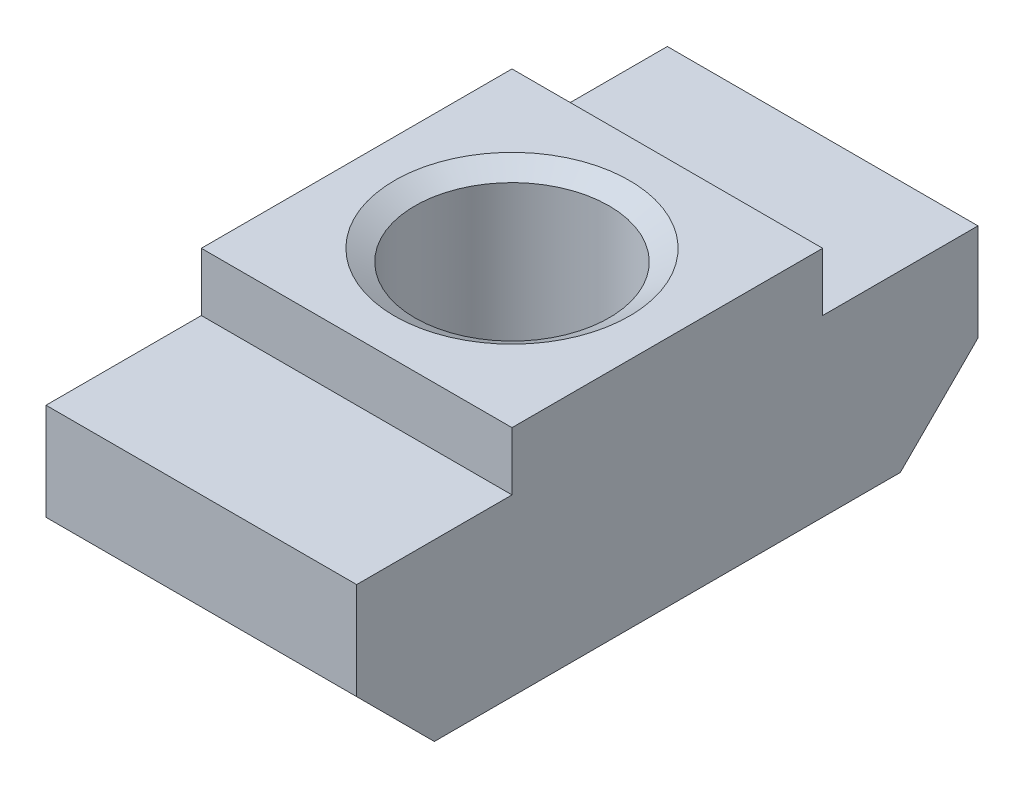
SolidWorks part; units mm, degrees
material "Acciaio al carbonio semplice"
ref_plane "Piano frontale" through (0, 0, 0) normal (0, 0, 1) x (1, 0, 0)
ref_plane "Piano superiore" through (0, 0, 0) normal (0, 1, 0) x (1, 0, 0)
ref_plane "Piano destro" through (0, 0, 0) normal (1, 0, 0) x (0, 0, -1)
sketch "Schizzo1" plane through (0, 0, 0) normal (0, 0, 1) x (1, 0, 0)
  line L1 (-4, 0) -> (-4, 6)
  line L2 (-4, 0) -> (4, 0)
  line L5 (-4, 6) -> (4, 6)
  line L6 (0, -16.3778) -> (0, 28.5715) construction
  line L7 (4, 0) -> (4, 6)
  point P11 (0, 0)
  point P15 (0, 6)
  dimension "D1" = 8
  dimension "D3" = 6
extrude "Estrusione-Estrusione1" add sketch "Schizzo1" along normal blind 16
ref_point "Punto1"
hole_wizard "Foro filettato M6-1" positions "Schizzo3" profile "Schizzo2" tap size "M6" standard "ISO" end condition through all
sketch "Schizzo3" plane through (0, 6, 0) normal (0, 1, 0) x (1, 0, 0)
  point P0 (0, -8)
cosmetic thread "Filettatura del foro1" parameters "D2"=6
sketch "Schizzo2" plane through (0, 6, 8) normal (1, 0, 0) x (0, 0, 1)
  line L0 (0, 0) -> (0, 6)
  line L1 (0, 6) -> (2.5, 6)
  line L2 (2.5, 6) -> (2.5, 0.3031)
  line L3 (2.5, 0.3031) -> (3.025, 0)
  line L5 (3.025, 0) -> (0, 0)
  line L6 (-2.5, 0.3031) -> (-3.025, 0) construction
  line L11 (0, -6.35) -> (0, 107.95) construction
  dimension "Thru Tap Drill Dia." = 5
  dimension "Thru Tap Drill Depth" = 6
  dimension "Near C'Sink Dia." = 6.05
  dimension "Near C'Sink Angle" = 120
sketch "Schizzo4" plane through (-4, 0, 0) normal (-1, 0, 0) x (0, 0, 1)
  line L0 (0, 0) -> (0, 2)
  line L3 (0, 6) -> (0, 0) construction
  line L4 (0, 2) -> (2, 0)
  line L6 (16, 0) -> (0, 0) construction
  line L7 (2, 0) -> (0, 0)
  line L8 (16, 0) -> (16, 2)
  line L10 (16, 6) -> (16, 0) construction
  line L11 (16, 2) -> (14, 0)
  line L12 (14, 0) -> (16, 0)
  line L13 (16, 4.5) -> (12, 4.5)
  line L14 (12, 4.5) -> (12, 6)
  line L15 (16, 6) -> (0, 6) construction
  line L16 (12, 6) -> (16, 6)
  line L17 (16, 6) -> (16, 4.5)
  line L18 (0, 4.5) -> (4, 4.5)
  line L19 (4, 4.5) -> (4, 6)
  line L20 (4, 6) -> (0, 6)
  line L21 (0, 6) -> (0, 4.5)
  line L22 (8, 6) -> (8, 0) construction
  dimension "D1" = 1.5
  dimension "D2" = 2
  dimension "D3" = 8
extrude "Taglio-Estrusione1" cut sketch "Schizzo4" against normal blind 10
